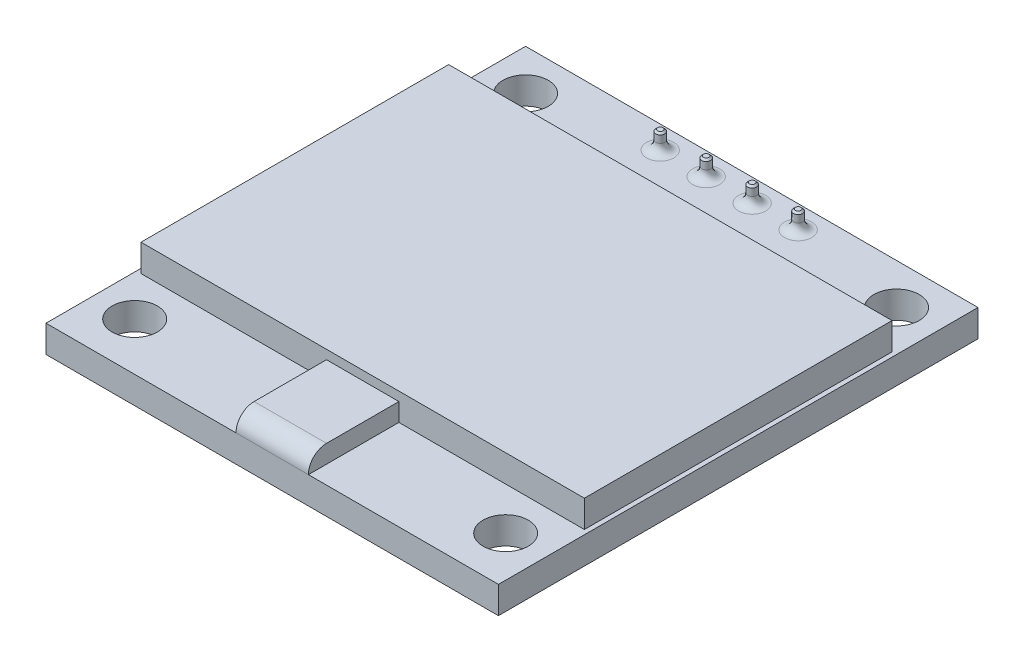
SolidWorks part; units mm, degrees
ref_plane "Front Plane" through (0, 0, 0) normal (0, 0, 1) x (1, 0, 0)
ref_plane "Top Plane" through (0, 0, 0) normal (0, 1, 0) x (1, 0, 0)
ref_plane "Right Plane" through (0, 0, 0) normal (1, 0, 0) x (0, 0, -1)
sketch "Sketch1" plane through (0, 0, 0) normal (0, 1, 0) x (1, 0, 0)
  line L1 (-12.5, -13.25) -> (12.5, -13.25)
  line L2 (-12.5, -13.25) -> (-12.5, 13.25)
  line L3 (-12.5, 13.25) -> (12.5, 13.25)
  line L4 (12.5, -13.25) -> (12.5, 13.25)
  line L5 (-12.5, -13.25) -> (12.5, 13.25) construction
  line L6 (-12.5, 13.25) -> (12.5, -13.25) construction
  point P0 (0, 0)
  dimension "D1" = 26.5
  dimension "D2" = 25
extrude "Boss-Extrude1" add sketch "Sketch1" along normal blind 1.5
sketch "Sketch2" plane through (0, 1.5, 0) normal (0, 1, 0) x (1, 0, 0)
  line L0 (0, 13.25) -> (0, -13.25) construction
  line L1 (12.5, 13.25) -> (-12.5, 13.25) construction
  line L2 (-12.5, -13.25) -> (12.5, -13.25) construction
  line L4 (-12.25, -8.25) -> (12.25, -8.25)
  line L5 (-12.25, -8.25) -> (-12.25, 8.75)
  line L6 (-12.25, 8.75) -> (12.25, 8.75)
  line L7 (12.25, -8.25) -> (12.25, 8.75)
  line L8 (-12.25, -8.25) -> (12.25, 8.75) construction
  line L9 (-12.25, 8.75) -> (12.25, -8.25) construction
  point P6 (0, 0.25)
  point P12 (0, 0)
  point P13 (0, -3.3378)
  dimension "D1" = 17
  dimension "D2" = 24.5
  dimension "D3" = 5
extrude "Boss-Extrude2" add sketch "Sketch2" along normal blind 1.5
sketch "Sketch3" plane through (0, 1.5, 0) normal (0, 1, 0) x (1, 0, 0)
  line L0 (-11.5, -13.25) -> (-11.5, 13.25) construction
  line L1 (-12.5, -13.25) -> (12.5, -13.25) construction
  line L2 (12.5, 13.25) -> (-12.5, 13.25) construction
  line L3 (-12.5, -11.85) -> (12.5, -11.85) construction
  line L4 (-12.5, 13.25) -> (-12.5, -13.25) construction
  line L5 (12.5, -13.25) -> (12.5, 13.25) construction
  circle A0 centre (-10.25, -10.6) radius 1.25
  dimension "D3" = 2.5
  dimension "D1" = 1.4
  dimension "D2" = 1
extrude "Cut-Extrude1" cut sketch "Sketch3" against normal blind 7.5
mirror "Mirror1" about plane through (0, 0, 0) normal (1, 0, 0) of "Cut-Extrude1"
sketch "Sketch4" plane through (0, 1.5, 0) normal (0, 1, 0) x (1, 0, 0)
  line L0 (-11.5, 13.25) -> (-11.5, -13.25) construction
  line L1 (12.5, 13.25) -> (-12.5, 13.25) construction
  line L2 (-12.5, -13.25) -> (12.5, -13.25) construction
  line L3 (-12.5, 12.25) -> (12.5, 12.25) construction
  line L4 (-12.5, 13.25) -> (-12.5, -13.25) construction
  line L5 (12.5, -13.25) -> (12.5, 13.25) construction
  circle A0 centre (-10.25, 11) radius 1.25
  dimension "D3" = 2.5
  dimension "D1" = 1
  dimension "D2" = 1
extrude "Cut-Extrude2" cut sketch "Sketch4" against normal blind 7.5
mirror "Mirror2" about plane through (0, 0, 0) normal (1, 0, 0) of "Cut-Extrude2"
sketch "Sketch5" plane through (0, 1.5, 0) normal (0, 1, 0) x (1, 0, 0)
  line L0 (0, 13.25) -> (0, -13.25) construction
  line L1 (12.5, 13.25) -> (-12.5, 13.25) construction
  line L2 (-12.5, -13.25) -> (12.5, -13.25) construction
  line L3 (-12.25, -8.25) -> (12.25, -8.25) construction
  line L4 (-2, -13.25) -> (2, -13.25)
  line L5 (-2, -13.25) -> (-2, -8.25)
  line L6 (-2, -8.25) -> (2, -8.25)
  line L7 (2, -13.25) -> (2, -8.25)
  line L8 (-2, -13.25) -> (2, -8.25) construction
  line L9 (-2, -8.25) -> (2, -13.25) construction
  point P6 (0, -10.75)
  dimension "D1" = 4
extrude "Boss-Extrude3" add sketch "Sketch5" along normal blind 1
fillet "Fillet1" radius 1 1 edges at (0, 2.5, 13.25)
sketch "Sketch6" plane through (0, 1.5, 0) normal (0, 1, 0) x (1, 0, 0)
  line L0 (0, 13.25) -> (0, -13.25) construction
  line L1 (12.5, 13.25) -> (-12.5, 13.25) construction
  line L2 (2, -13.25) -> (-2, -13.25) construction
  line L3 (-3.81, 13.25) -> (-3.81, -13.25) construction
  line L4 (-12.5, -13.25) -> (-2, -13.25) construction
  line L5 (-12.5, 12.25) -> (12.5, 12.25) construction
  line L6 (-12.5, 13.25) -> (-12.5, -13.25) construction
  line L7 (12.5, -13.25) -> (12.5, 13.25) construction
  circle A0 centre (-3.81, 12) radius 0.25
  point P18 (0, 0)
  dimension "D2" = 0.5
  dimension "D1" = 3.81
  dimension "D3" = 1
extrude "Boss-Extrude4" add sketch "Sketch6" along normal blind 1 and the other way blind 9.6
chamfer "Chamfer1" distance 0.1 angle 45 1 edges at (-3.81, 2.5, -11.75)
fillet "Fillet2" radius 0.5 1 edges at (-3.81, 1.5, -12.25)
pattern_linear "LPattern1" count 4 spacing 2.54 along (1, 0, 0) of "Boss-Extrude4", "Chamfer1", "Fillet2"
sketch "Sketch7" plane through (0, 0, 0) normal (0, -1, 0) x (1, 0, 0)
  line L0 (0, -13.25) -> (0, 13.25) construction
  line L1 (12.5, -13.25) -> (-12.5, -13.25) construction
  line L2 (-12.5, 13.25) -> (12.5, 13.25) construction
  line L4 (5, -13.25) -> (-5, -13.25)
  line L5 (5, -13.25) -> (5, -10.75)
  line L6 (5, -10.75) -> (-5, -10.75)
  line L7 (-5, -13.25) -> (-5, -10.75)
  line L8 (5, -13.25) -> (-5, -10.75) construction
  line L9 (5, -10.75) -> (-5, -13.25) construction
  point P6 (0, -12)
  dimension "D1" = 10
  dimension "D2" = 2.5
extrude "Boss-Extrude5" add sketch "Sketch7" along normal blind 2.5
fillet "Fillet3" radius 0.75 4 edges at (-5, -1.25, -10.75) (-5, -1.25, -13.25) (5, -1.25, -10.75) (5, -1.25, -13.25)
